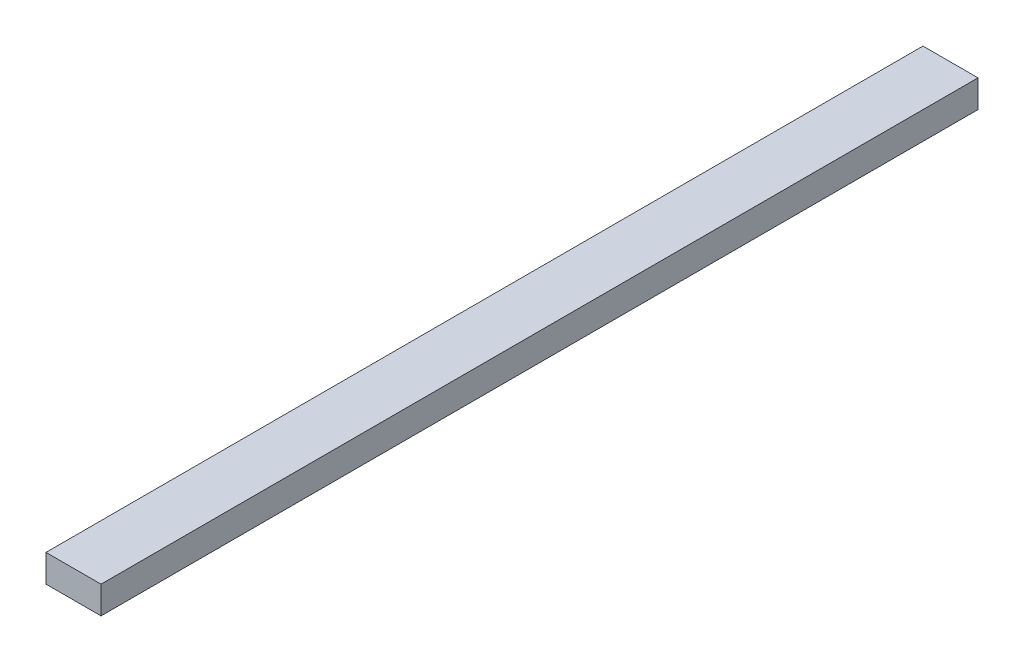
SolidWorks part; units mm, degrees
ref_plane "Front" through (0, 0, 0) normal (0, 0, 1) x (1, 0, 0)
ref_plane "Top" through (0, 0, 0) normal (0, 1, 0) x (1, 0, 0)
ref_plane "Right" through (0, 0, 0) normal (1, 0, 0) x (0, 0, -1)
sketch "Эскиз1" plane through (0, 0, 0) normal (0, 0, 1) x (1, 0, 0)
  line L1 (-23.9098, 22.6316) -> (56.0902, 22.6316)
  line L2 (-23.9098, 22.6316) -> (-23.9098, -17.3684)
  line L3 (-23.9098, -17.3684) -> (56.0902, -17.3684)
  line L4 (56.0902, 22.6316) -> (56.0902, -17.3684)
  dimension "D1" = 40
  dimension "D2" = 80
extrude "Бобышка-Вытянуть1" add sketch "Эскиз1" along normal blind 1275
